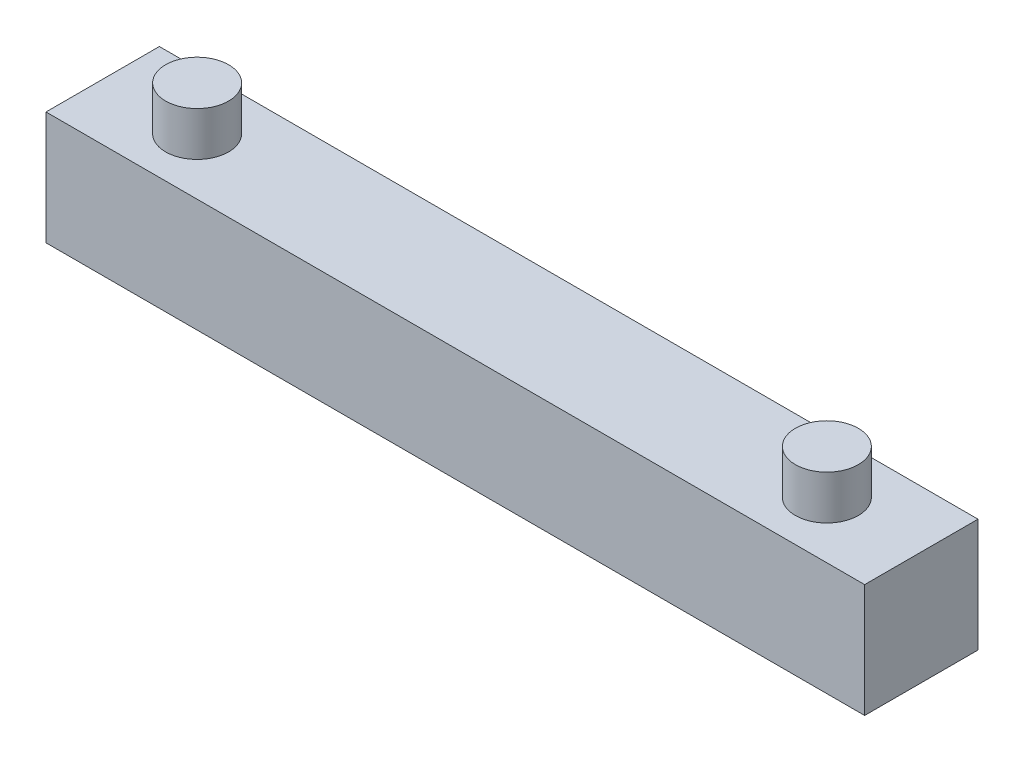
SolidWorks part; units mm, degrees
ref_plane "Front Plane" through (0, 0, 0) normal (0, 0, 1) x (1, 0, 0)
ref_plane "Top Plane" through (0, 0, 0) normal (0, 1, 0) x (1, 0, 0)
ref_plane "Right Plane" through (0, 0, 0) normal (1, 0, 0) x (0, 0, -1)
sketch "Sketch2" plane through (0, 0, 0) normal (0, 1, 0) x (1, 0, 0)
  line L0 (0, 4.5) -> (0, -4.5) construction
  line L1 (-32.5, 4.5) -> (32.5, 4.5)
  line L2 (-32.5, 4.5) -> (-32.5, -4.5)
  line L3 (-32.5, -4.5) -> (32.5, -4.5)
  line L4 (32.5, 4.5) -> (32.5, -4.5)
  line L5 (-32.5, 4.5) -> (32.5, -4.5) construction
  line L6 (-32.5, -4.5) -> (32.5, 4.5) construction
  line L7 (0, 0) -> (-25, 0) construction
  line L8 (0, 0) -> (25, 0) construction
  point P0 (0, 0)
  point P10 (0, 0)
  dimension "D1" = 65
  dimension "D2" = 9
extrude "Boss-Extrude1" add sketch "Sketch2" along normal blind 9
sketch "Sketch3" plane through (0, 9, 0) normal (0, 1, 0) x (1, 0, 0)
  line L0 (0, 0) -> (25, 0) construction
  line L1 (0, 0) -> (-25, 0) construction
  circle A0 centre (-25, 0) radius 2.5
extrude "Boss-Extrude2" add sketch "Sketch3" along normal blind 3.5
sketch "Sketch4" plane through (0, 9, 0) normal (0, 1, 0) x (1, 0, 0)
  line L0 (0, 0) -> (25, 0) construction
  circle A0 centre (25, 0) radius 2.5
extrude "Boss-Extrude3" add sketch "Sketch4" along normal blind 3.5
